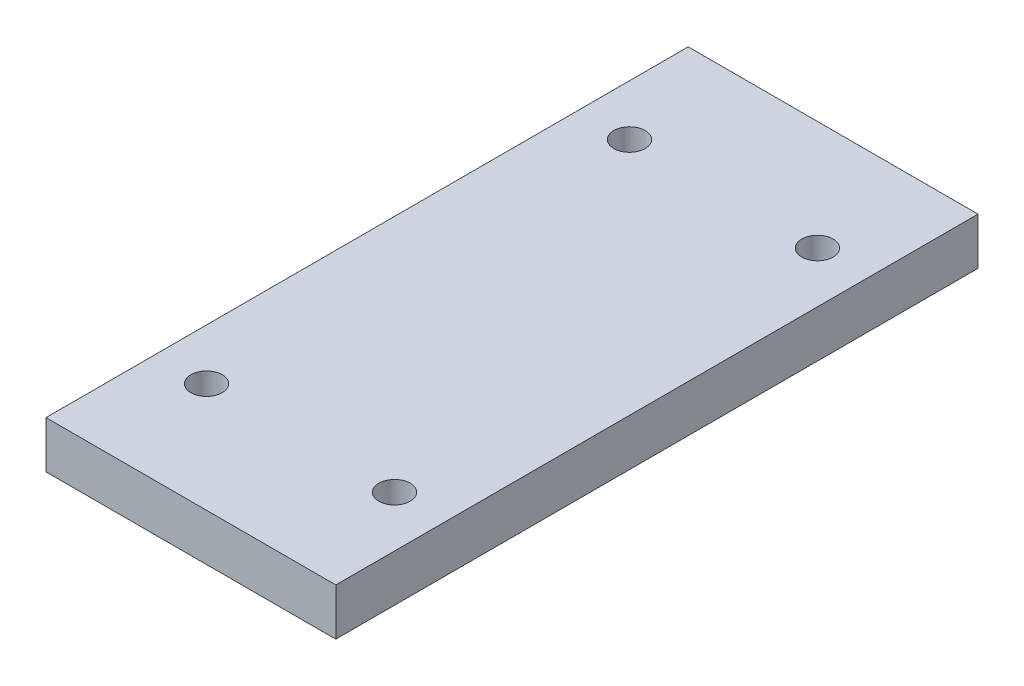
SolidWorks part; units mm, degrees
ref_plane "Alzado" through (0, 0, 0) normal (0, 0, 1) x (1, 0, 0)
ref_plane "Planta" through (0, 0, 0) normal (0, 1, 0) x (1, 0, 0)
ref_plane "Vista lateral" through (0, 0, 0) normal (1, 0, 0) x (0, 0, -1)
sketch "Croquis1" plane through (0, 0, 0) normal (0, 1, 0) x (1, 0, 0)
  line L0 (-6.2544, 19.9383) -> (-6.2544, -21.0617)
  line L1 (-6.2544, -21.0617) -> (12.2456, -21.0617)
  line L2 (12.2456, -21.0617) -> (12.2456, 19.9383)
  line L3 (12.2456, 19.9383) -> (-6.2544, 19.9383)
  circle A0 centre (-3.0044, 12.9383) radius 1
  circle A1 centre (8.9956, 12.9383) radius 1
  circle A2 centre (-3.004, -14.0617) radius 0.9998
  circle A3 centre (8.9956, -14.0617) radius 1
extrude "Saliente-Extruir1" add sketch "Croquis1" along normal blind 3
